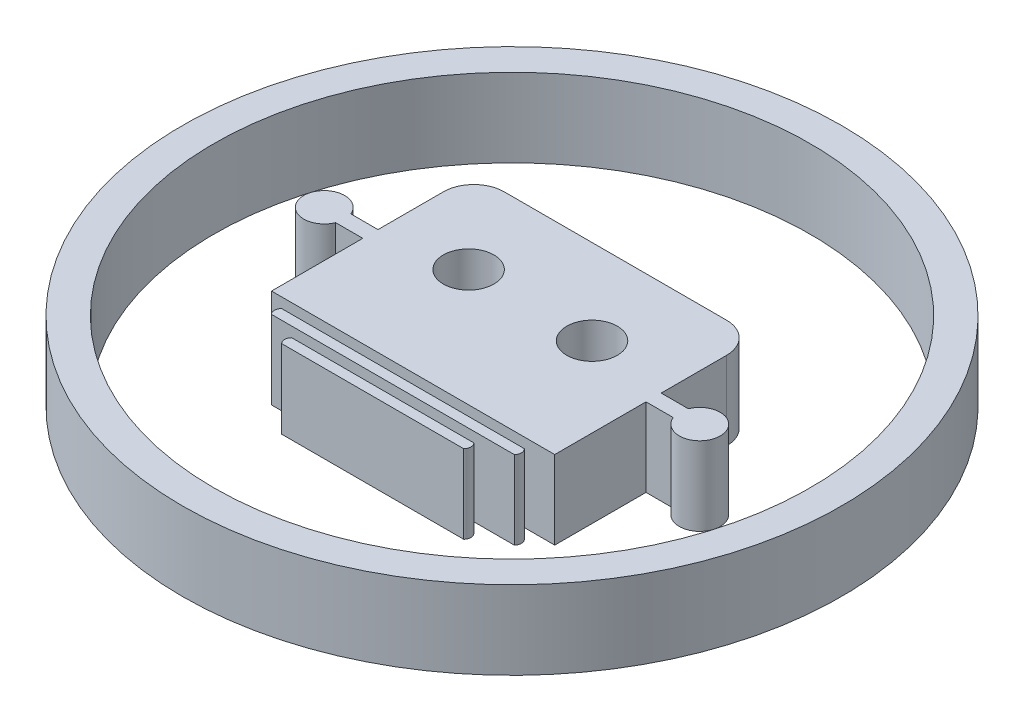
SolidWorks part; units mm, degrees
ref_plane "Front Plane" through (0, 0, 0) normal (0, 0, 1) x (1, 0, 0)
ref_plane "Top Plane" through (0, 0, 0) normal (0, 1, 0) x (1, 0, 0)
ref_plane "Right Plane" through (0, 0, 0) normal (1, 0, 0) x (0, 0, -1)
sketch "Sketch1" plane through (0, 0, 0) normal (0, 1, 0) x (1, 0, 0)
  line L0 (-35.6565, 106.4543) -> (-35.6565, 111.2038) construction
  line L1 (-55.1565, 106.4543) -> (-16.1565, 106.4543) construction
  line L2 (-55.1565, 106.4543) -> (-55.1565, 67.4543) construction
  line L3 (-55.1565, 67.4543) -> (-16.1565, 67.4543) construction
  line L4 (-16.1565, 106.4543) -> (-16.1565, 67.4543) construction
  circle A2 centre (-35.6565, 86.8647) radius 19
  circle A3 centre (-35.6565, 86.8647) radius 21
  line B0 (-44.6796, 80.5643) -> (-44.6796, 86.3813)
  line B1 (-42.746, 93.4543) -> (-28.567, 93.4543)
  line B2 (-26.6335, 91.5208) -> (-26.6335, 87.3481)
  line B3 (-26.6335, 87.3481) -> (-24.9009, 87.3481)
  line B4 (-24.9009, 86.3813) -> (-26.6335, 86.3813)
  line B5 (-26.6335, 86.3813) -> (-26.6335, 80.5643)
  line B6 (-26.6335, 80.5643) -> (-44.6796, 80.5643)
  line B7 (-46.4122, 87.3481) -> (-44.6796, 87.3481)
  line B8 (-44.6796, 86.3813) -> (-46.4122, 86.3813)
  line B9 (-43.3905, 79.9198) -> (-27.9225, 79.9198)
  line B10 (-43.3905, 79.2753) -> (-27.9225, 79.2753)
  line B11 (-41.457, 78.6308) -> (-29.856, 78.6308)
  line B12 (-41.457, 77.9863) -> (-29.856, 77.9863)
  line B13 (-44.6796, 87.3481) -> (-44.6796, 91.5208)
  line B14 (-35.6565, 86.8647) -> (-35.6565, 86.008) construction
  line B15 (-36.6157, 86.8647) -> (-34.909, 86.8647) construction
  circle B16 centre (-39.5884, 88.0327) radius 1.6113
  circle B17 centre (-31.7247, 88.0327) radius 1.6113
  arc B18 (-46.4122, 87.3481) -> (-46.4122, 86.3813) centre (-47.6224, 86.8647) ccw
  arc B19 (-24.9009, 86.3813) -> (-24.9009, 87.3481) centre (-23.6906, 86.8647) ccw
  arc B20 (-42.746, 93.4543) -> (-44.6796, 91.5208) centre (-42.746, 91.5208) ccw
  arc B21 (-26.6335, 91.5208) -> (-28.567, 93.4543) centre (-28.567, 91.5208) ccw
  arc B22 (-43.3905, 79.9198) -> (-43.3905, 79.2753) centre (-43.0683, 79.5975) ccw
  arc B23 (-41.457, 78.6308) -> (-41.457, 77.9863) centre (-41.1348, 78.3085) ccw
  arc B24 (-29.856, 78.6308) -> (-29.856, 77.9863) centre (-30.1783, 78.3085) cw
  arc B25 (-27.9225, 79.9198) -> (-27.9225, 79.2753) centre (-28.2447, 79.5975) cw
  dimension "D1" = 39
  dimension "D4" = 38
  dimension "D5" = 2
  dimension "D2" = 39
  dimension "D3" = 13
sketch_block_instance "Block3-1"
sketch_block "Block3"
extrude "Boss-Extrude1" add sketch "Sketch1" along normal blind 5 contours A3 A2 | B2 B21 B1 B20 B13 B7 B18 B8 B0 B6 B5 B4 B19 B3 B16 B17 | B24 B11 B23 B12 | B25 B9 B22 B10
